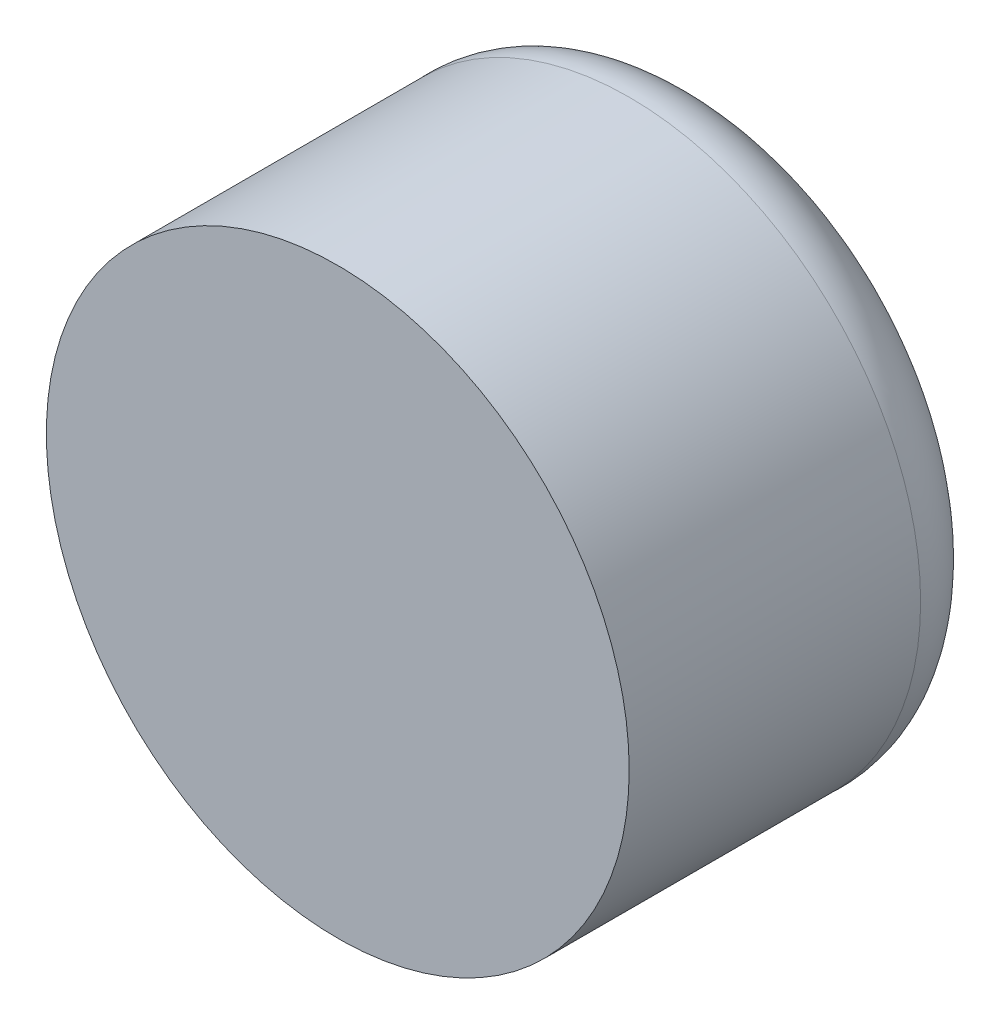
SolidWorks part; units mm, degrees
ref_plane "Front Plane" through (0, 0, 0) normal (0, 0, 1) x (1, 0, 0)
ref_plane "Top Plane" through (0, 0, 0) normal (0, 1, 0) x (1, 0, 0)
ref_plane "Right Plane" through (0, 0, 0) normal (1, 0, 0) x (0, 0, -1)
sketch "Sketch1" plane through (0, 0, 0) normal (0, 0, 1) x (1, 0, 0)
  circle A0 centre (0, 0) radius 250
extrude "Boss-Extrude1" add sketch "Sketch1" along normal blind 250
sketch "Sketch2" plane through (0, 0, 0) normal (1, 0, 0) x (0, 0, -1)
  line L0 (0, 0) -> (100, 0)
  line L1 (0, 0) -> (0, 250)
  spline S0 degree 3 poles (0, 250) (99.7143, 257.4174) (98.7571, 27.6383) (100, 0) knots 0 0 0 0 1 1 1 1
  point P4 (0, 0)
  point P6 (0, 0)
  point P8 (83.132, 161.785)
  point P9 (0, 0)
  point P10 (0, 0)
  point P11 (81.8142, 159.8316)
revolve "Revolve1" add sketch "Sketch2" angle 360 about L0
